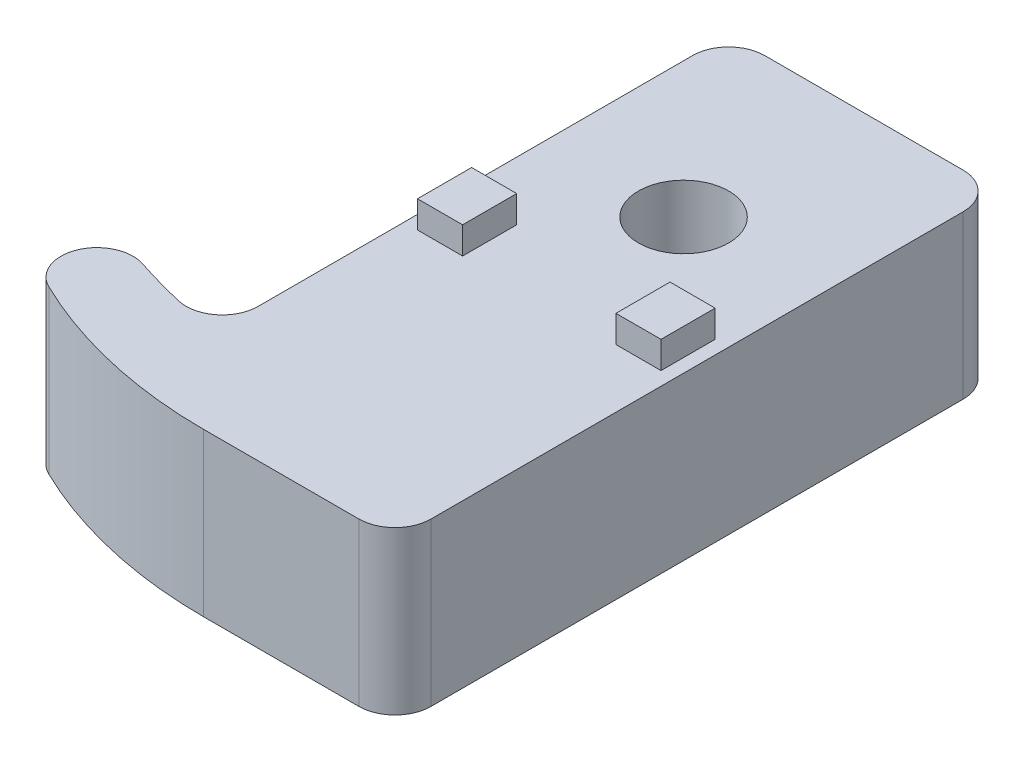
SolidWorks part; units mm, degrees
ref_plane "前视基准面" through (0, 0, 0) normal (0, 0, 1) x (1, 0, 0)
ref_plane "上视基准面" through (0, 0, 0) normal (0, 1, 0) x (1, 0, 0)
ref_plane "右视基准面" through (0, 0, 0) normal (1, 0, 0) x (0, 0, -1)
other "Configuration Table"
sketch "草图1" plane through (0, 0, 0) normal (0, 1, 0) x (1, 0, 0)
  line L0 (-2.3828, 33.5) -> (8.6172, 33.5)
  line L1 (10.6172, 31.5) -> (10.6172, 2)
  line L2 (8.6172, 0) -> (0, 0)
  line L5 (-4.3828, 7.4211) -> (-4.3828, 31.5)
  arc A0 (0, 0) -> (-11.1311, 2.5577) centre (0, 25.5) cw
  arc A1 (-6.8364, 5.4732) -> (-9.6333, 6.257) centre (0.5711, 37.2861) cw
  arc A2 (-11.1311, 2.5577) -> (-9.6333, 6.257) centre (-10.2581, 4.3571) cw
  arc A3 (-6.8364, 5.4732) -> (-4.3828, 7.4211) centre (-6.3828, 7.4211) ccw
  arc A4 (10.6172, 2) -> (8.6172, 0) centre (8.6172, 2) cw
  arc A5 (8.6172, 33.5) -> (10.6172, 31.5) centre (8.6172, 31.5) cw
  arc A6 (-2.3828, 33.5) -> (-4.3828, 31.5) centre (-2.3828, 31.5) ccw
  circle A7 centre (3.1172, 23.5) radius 2.5
  point P15 (10.6172, 0)
  point P18 (10.6172, 33.5)
  point P21 (-4.3828, 33.5)
  point P24 (3.1172, 33.5)
  dimension "D5" = 25.5
  dimension "D3" = 2
  dimension "D4" = 2
  dimension "D6" = 5
  dimension "D1" = 15
  dimension "D2" = 33.5
  dimension "D7" = 10
  dimension "D8" = 8.6172
extrude "凸台-拉伸1" add sketch "草图1" along normal blind 9
sketch "草图3" plane through (0, 9, 0) normal (0, 1, 0) x (1, 0, 0)
  line L0 (-4.3828, 31.5) -> (-4.3828, 7.4211) construction
  line L1 (-3.6328, 18.5) -> (-1.1328, 18.5)
  line L2 (-3.6328, 18.5) -> (-3.6328, 15.5)
  line L3 (-3.6328, 15.5) -> (-1.1328, 15.5)
  line L4 (-1.1328, 18.5) -> (-1.1328, 15.5)
  line L5 (3.1172, 23.5) -> (3.1172, 23.4622) construction
  line L6 (7.3672, 18.5) -> (7.3672, 15.5)
  line L7 (9.8672, 15.5) -> (7.3672, 15.5)
  line L8 (9.8672, 18.5) -> (9.8672, 15.5)
  line L9 (9.8672, 18.5) -> (7.3672, 18.5)
  circle A0 centre (3.1172, 23.5) radius 2.5 construction
  circle A1 centre (3.1172, 23.5) radius 2.5 construction
  dimension "D1" = 2.5
  dimension "D2" = 3
  dimension "D3" = 0.75
  dimension "D4" = 5
extrude "凸台-拉伸2" add sketch "草图3" along normal blind 1.5
sketch "草图5" plane through (0, 9, 0) normal (0, 1, 0) x (1, 0, 0)
  line L0 (8.6172, 33.5) -> (-2.3828, 33.5) construction
  line L1 (-4.3828, 31.5) -> (8.6172, 31.5)
  line L2 (-4.3828, 31.5) -> (-4.3828, 30)
  line L3 (-4.3828, 30) -> (8.6172, 30)
  line L4 (8.6172, 31.5) -> (8.6172, 30)
  line L6 (-4.3828, 31.5) -> (-4.3828, 7.4211) construction
  dimension "D1" = 1.5
  dimension "D2" = 13
  dimension "D3" = 2
extrude "切除-拉伸1" cut sketch "草图5" against normal up to next
sketch "草图6" plane through (0, 9, 0) normal (0, 1, 0) x (1, 0, 0)
  line L0 (8.6172, 30) -> (8.6172, 31.5) construction
  line L1 (-4.3828, 30) -> (8.6172, 30) construction
  line L2 (8.6172, 31.5) -> (-4.3828, 31.5) construction
  line L3 (8.6172, 30) -> (8.6172, 31.5)
  line L4 (-4.3828, 30) -> (8.6172, 30)
  line L5 (8.6172, 31.5) -> (-4.3828, 31.5)
  line L6 (-4.3828, 31.5) -> (-4.3828, 30)
extrude "凸台-拉伸3" add sketch "草图6" against normal blind 1
sketch "草图7" plane through (0, 0, -33.5) normal (0, 0, -1) x (-1, 0, 0)
  line L0 (-8.6172, 9) -> (-8.6172, 0) construction
  line L1 (-8.6172, 2.5) -> (4.3828, 2.5)
  line L2 (-8.6172, 2.5) -> (-8.6172, 1.5)
  line L3 (-8.6172, 1.5) -> (4.3828, 1.5)
  line L4 (4.3828, 2.5) -> (4.3828, 1.5)
  line L5 (4.3828, 9) -> (4.3828, 0) construction
  line L6 (-8.6172, 0) -> (2.3828, 0) construction
  dimension "D1" = 1
  dimension "D2" = 1.5
extrude "切除-拉伸2" cut sketch "草图7" against normal up to next
